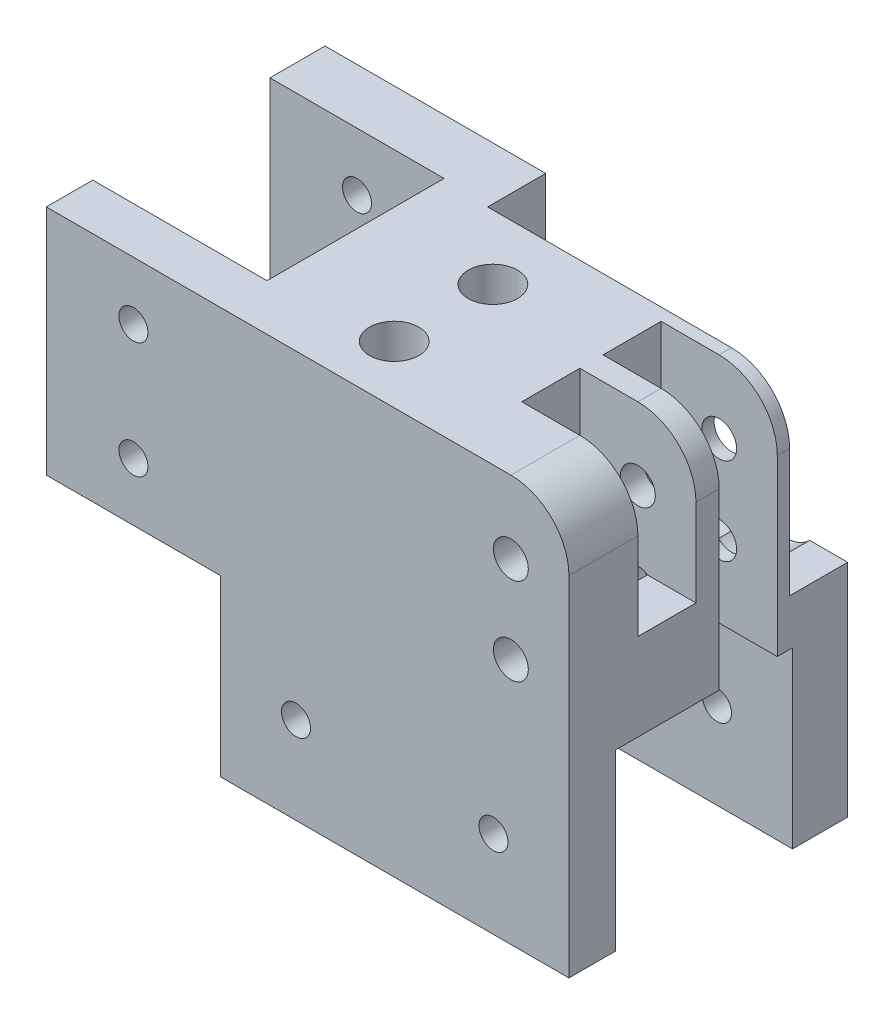
SolidWorks part; units mm, degrees
ref_plane "Front Plane" through (0, 0, 0) normal (0, 0, 1) x (1, 0, 0)
ref_plane "Top Plane" through (0, 0, 0) normal (0, 1, 0) x (1, 0, 0)
ref_plane "Right Plane" through (0, 0, 0) normal (1, 0, 0) x (0, 0, -1)
sketch "Esboço1" plane through (0, 0, 0) normal (0, 0, 1) x (1, 0, 0)
  line L0 (440, 72.2122) -> (440, 102.2122) construction
  line L1 (440, 72.2122) -> (380, 72.2122)
  line L2 (470, 102.2122) -> (470, 142.2122)
  line L3 (470, 142.2122) -> (390, 142.2122)
  line L4 (380, 72.2122) -> (380, 132.2122)
  line L5 (440, 102.2122) -> (470, 102.2122) construction
  line L6 (440, 72.2122) -> (440, 102.2122)
  line L7 (440, 102.2122) -> (470, 102.2122)
  line L9 (440, 87.2122) -> (380, 87.2122) construction
  line L10 (455, 102.2122) -> (455, 142.2122) construction
  arc A0 (390, 142.2122) -> (380, 132.2122) centre (390, 132.2122) ccw
  dimension "D1" = 10
  dimension "D2" = 40
  dimension "D3" = 60
extrude "Ressalto-extrusão1" add sketch "Esboço1" along normal blind 8 contours L4 A0 L3 L2 L7 L6 L1
hole_wizard "Broca de rosquear para tarraxa de M6x1.01" positions "Esboço2" profile "Esboço3" hole size "M6x1.0" standard "Ansi Metric" end condition through all
sketch "Esboço2" plane through (0, 0, 8) normal (0, 0, 1) x (1, 0, 0)
  line L0 (440, 87.2122) -> (380, 87.2122) construction
  line L1 (455, 102.2122) -> (455, 142.2122) construction
  line L2 (380, 72.2122) -> (380, 132.2122) construction
  line L3 (440, 72.2122) -> (440, 102.2122) construction
  line L4 (470, 142.2122) -> (390, 142.2122) construction
  point P0 (393, 87.2122)
  point P4 (427, 87.2122)
  point P6 (455, 112.2122)
  point P10 (455, 132.2122)
  dimension "D1" = 13
  dimension "D2" = 13
  dimension "D3" = 10
  dimension "D4" = 10
sketch "Esboço3" plane through (393, 87.2122, 8) normal (1, 0, 0) x (0, -1, 0)
  line L0 (0, 0) -> (0, 8)
  line L1 (0, 8) -> (2.5, 8)
  line L2 (2.5, 8) -> (2.5, 0)
  line L5 (2.5, 0) -> (0, 0)
  line L11 (0, -6.35) -> (0, 107.95) construction
  dimension "Thru Hole Dia." = 5
  dimension "Thru Hole Depth" = 8
sketch "Esboço4" plane through (0, 0, 0) normal (0, 0, -1) x (-1, 0, 0)
  line L0 (-470, 142.2122) -> (-390, 142.2122) construction
  line L1 (-390, 142.2122) -> (-440, 142.2122)
  line L2 (-380, 132.2122) -> (-380, 102.2122)
  line L3 (-380, 102.2122) -> (-440, 102.2122)
  line L4 (-440, 142.2122) -> (-440, 102.2122)
  line L5 (-380, 72.2122) -> (-380, 132.2122) construction
  arc A0 (-390, 142.2122) -> (-380, 132.2122) centre (-390, 132.2122) cw
  point P11 (-380, 142.2122)
  dimension "D1" = 10
extrude "Ressalto-extrusão2" add sketch "Esboço4" along normal blind 30
sketch "Esboço6" plane through (380, 0, 0) normal (-1, 0, 0) x (0, 0, 1)
  line L0 (-30, 142.2122) -> (0, 142.2122) construction
  line L1 (-27.8749, 102.2122) -> (-17.8749, 102.2122)
  line L2 (-27.8749, 102.2122) -> (-27.8749, 142.2122)
  line L3 (-27.8749, 142.2122) -> (-17.8749, 142.2122)
  line L4 (-17.8749, 102.2122) -> (-17.8749, 142.2122)
  line L5 (-13.8749, 117.2122) -> (-3.8749, 117.2122)
  line L6 (-13.8749, 117.2122) -> (-13.8749, 142.2122)
  line L7 (-13.8749, 142.2122) -> (-3.8749, 142.2122)
  line L8 (-3.8749, 117.2122) -> (-3.8749, 142.2122)
  dimension "D1" = 10
  dimension "D2" = 10
  dimension "D3" = 25
  dimension "D4" = 40
  dimension "D5" = 4
extrude "Corte-extrusão2" cut sketch "Esboço6" against normal blind 20
sketch "Esboço14" plane through (0, 0, -30) normal (0, 0, -1) x (-1, 0, 0)
  circle A2 centre (-390, 129.7122) radius 3
  circle A3 centre (-390, 129.7122) radius 3
  circle A5 centre (-390, 114.7122) radius 3
  circle A6 centre (-390, 114.7122) radius 3
  dimension "D1" = 0.5
  dimension "D2" = 0.5
extrude "Corte-extrusão6" cut sketch "Esboço14" against normal through all
sketch "Esboço15" plane through (0, 142.2122, 0) normal (0, 1, 0) x (1, 0, 0)
  circle A2 centre (420, 18.9024) radius 4.25
  circle A3 centre (420, 18.9024) radius 4.25
  circle A5 centre (420, 1.9024) radius 4.25
  circle A6 centre (420, 1.9024) radius 4.25
  dimension "D1" = 0
  dimension "D2" = 0
extrude "Corte-extrusão7" cut sketch "Esboço15" against normal up to surface (40 mm away) up to face at (400, 102.2122, -18.9374)
mirror "Espelhar1" about plane through (380, 72.2122, 8) normal (-1, 0, 0) of bodies 111
delete or keep bodies "Corpo-Excluir/Manter 1" type delete bodies bodies 111
sketch "Esboço16" plane through (0, 0, -30) normal (0, 0, -1) x (-1, 0, 0)
  line L0 (-320, 102.2122) -> (-380, 102.2122) construction
  line L1 (-320, 142.2122) -> (-328, 142.2122)
  line L2 (-320, 142.2122) -> (-320, 102.2122)
  line L3 (-320, 102.2122) -> (-328, 102.2122)
  line L4 (-328, 142.2122) -> (-328, 110.2122)
  line L5 (-380, 102.2122) -> (-380, 132.2122) construction
  line L6 (-380, 110.2122) -> (-373.455, 110.2122)
  line L7 (-380, 110.2122) -> (-380, 102.2122)
  line L8 (-380, 102.2122) -> (-328, 102.2122)
  line L10 (-365.321, 110.2122) -> (-328, 110.2122)
  arc A0 (-365.321, 110.2122) -> (-373.455, 110.2122) centre (-369.388, 114.2792) cw
  dimension "D1" = 8
  dimension "D2" = 8
extrude "Ressalto-extrusão3" add sketch "Esboço16" along normal blind 10
sketch "Esboço17" plane through (320, 0, 0) normal (-1, 0, 0) x (0, 0, 1)
  line L0 (-40, 142.2122) -> (0, 142.2122) construction
  line L1 (-40, 102.2122) -> (-30.5, 102.2122)
  line L2 (-40, 102.2122) -> (-40, 142.2122)
  line L3 (-40, 142.2122) -> (-30.5, 142.2122)
  line L4 (-30.5, 102.2122) -> (-30.5, 142.2122)
  line L5 (-30, 102.2122) -> (-30, 542.2122) construction
  dimension "D1" = 0.5
extrude "Ressalto-extrusão4" add sketch "Esboço17" along normal through all
sketch "Esboço18" plane through (0, 0, -30.5) normal (0, 0, 1) x (1, 0, 0)
  circle A10 centre (305, 112.2122) radius 2.5
  circle A11 centre (305, 112.2122) radius 2.5
  circle A13 centre (305, 132.2122) radius 2.5
  circle A14 centre (305, 132.2122) radius 2.5
  dimension "D1" = 0
  dimension "D2" = 0
extrude "Corte-extrusão8" cut sketch "Esboço18" against normal blind 10
sketch "Esboço19" plane through (0, 102.2122, 0) normal (0, -1, 0) x (1, 0, 0)
  line L0 (320, -100) -> (320, 470) construction
  line L1 (380, -40) -> (320, -40)
  line L2 (380, -40) -> (380, -30.5)
  line L3 (380, -30.5) -> (320, -30.5)
  line L4 (320, -40) -> (320, -30.5)
  line L5 (760, -30) -> (320, -30) construction
  dimension "D1" = 0.5
extrude "Ressalto-extrusão5" add sketch "Esboço19" along normal through all
fillet "Filete1" radius 5 1 edges at (328, 110.2122, -35)
sketch "Esboço20" plane through (0, 0, -30.5) normal (0, 0, 1) x (1, 0, 0)
  circle A2 centre (367, 87.2122) radius 2.5
  circle A3 centre (367, 87.2122) radius 2.5
  circle A5 centre (333, 87.2122) radius 2.5
  circle A6 centre (333, 87.2122) radius 2.5
  dimension "D1" = 0
  dimension "D2" = 0
extrude "Corte-extrusão9" cut sketch "Esboço20" against normal blind 10
